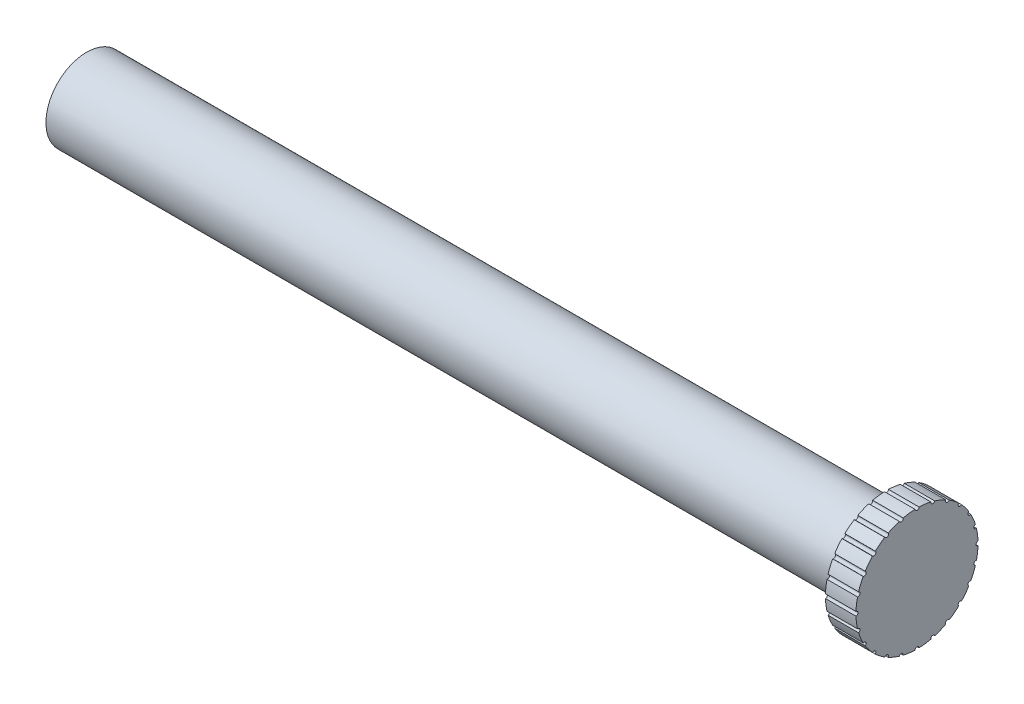
SolidWorks part; units mm, degrees
material "1060 Alloy"
ref_plane "Front Plane" through (0, 0, 0) normal (0, 0, 1) x (1, 0, 0)
ref_plane "Top Plane" through (0, 0, 0) normal (0, 1, 0) x (1, 0, 0)
ref_plane "Right Plane" through (0, 0, 0) normal (1, 0, 0) x (0, 0, -1)
sketch "Sketch1" plane through (0, 0, 0) normal (1, 0, 0) x (0, 0, -1)
  circle A0 centre (0, 0) radius 4
  dimension "D1" = 8
extrude "Boss-Extrude2" add sketch "Sketch1" along normal blind 78.63
sketch "Sketch2" plane through (78.63, 0, 0) normal (1, 0, 0) x (0, 0, -1)
  circle A0 centre (0, 0) radius 6
  dimension "D1" = 12
extrude "Boss-Extrude3" add sketch "Sketch2" along normal blind 3
sketch "Sketch3" plane through (81.63, 0, 0) normal (1, 0, 0) x (0, 0, -1)
  line L0 (-8.3009, 0) -> (10.599, 0) construction
  circle A0 centre (-6, 0) radius 0.2
  circle A1 centre (0, 0) radius 6 construction
  dimension "D1" = 0.4
extrude "Cut-Extrude1" cut sketch "Sketch3" against normal up to surface (3 mm away) up to face at (78.63, 0, -4)
pattern_circular "CirPattern1" count 25 every 15 about axis through (0, 0, -0.0033) along (1, 0, 0) of "Cut-Extrude1"
